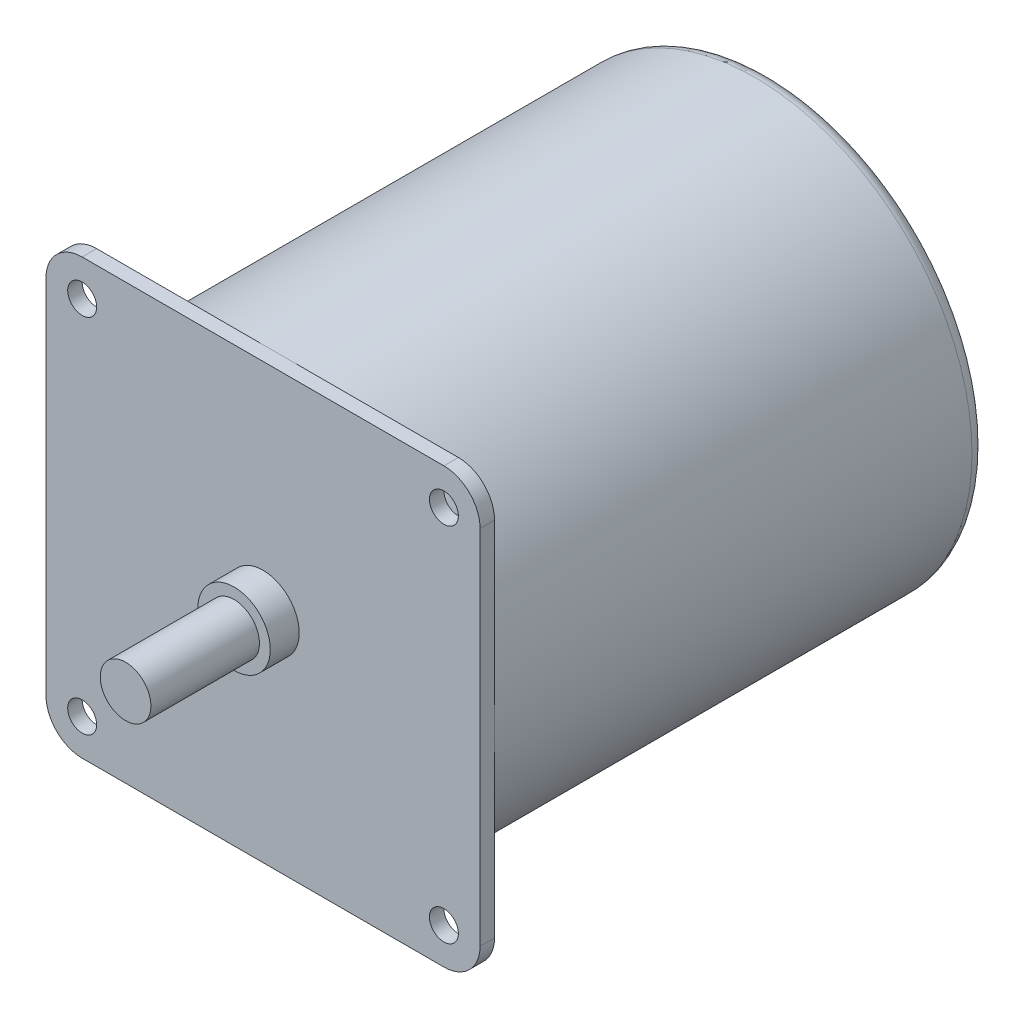
SolidWorks part; units mm, degrees
ref_plane "Front Plane" through (0, 0, 0) normal (0, 0, 1) x (1, 0, 0)
ref_plane "Top Plane" through (0, 0, 0) normal (0, 1, 0) x (1, 0, 0)
ref_plane "Right Plane" through (0, 0, 0) normal (1, 0, 0) x (0, 0, -1)
sketch "Sketch1" plane through (0, 0, 0) normal (0, 0, 1) x (1, 0, 0)
  circle A0 centre (0, 0) radius 30
  dimension "D1" = 60
extrude "Boss-Extrude1" add sketch "Sketch1" along normal blind 68
sketch "Sketch2" plane through (0, 0, 68) normal (0, 0, 1) x (1, 0, 0)
  line L0 (0, 33.5907) -> (0, -35.7587) construction
  line L1 (25, 30) -> (-25, 30)
  line L2 (30, 25) -> (30, -25)
  line L3 (25, -30) -> (-25, -30)
  line L4 (-30, 25) -> (-30, -25)
  line L5 (30, 30) -> (-30, -30) construction
  line L6 (30, -30) -> (-30, 30) construction
  line L7 (-22.9801, 0) -> (21.8103, 0) construction
  arc A1 (-25, -30) -> (-30, -25) centre (-25, -25) cw
  arc A2 (25, -30) -> (30, -25) centre (25, -25) ccw
  arc A3 (30, 25) -> (25, 30) centre (25, 25) ccw
  arc A4 (-25, 30) -> (-30, 25) centre (-25, 25) ccw
  circle A5 centre (-25, 25) radius 2
  circle A6 centre (25, 25) radius 2
  circle A7 centre (25, -25) radius 2
  circle A8 centre (-25, -25) radius 2
  point P0 (0, 0)
  dimension "D1" = 60
  dimension "D3" = 5
  dimension "D4" = 4
  dimension "D2" = 60
extrude "Boss-Extrude2" add sketch "Sketch2" along normal blind 2
fillet "Fillet1" radius 2 1 edges at (30, 0, 0)
sketch "Sketch3" plane through (0, 0, 70) normal (0, 0, 1) x (1, 0, 0)
  circle A0 centre (0, 0) radius 5
  dimension "D1" = 10
extrude "Boss-Extrude3" add sketch "Sketch3" along normal blind 4
sketch "Sketch4" plane through (0, 0, 74) normal (0, 0, 1) x (1, 0, 0)
  circle A0 centre (0, 0) radius 3.5
  dimension "D1" = 7
extrude "Boss-Extrude4" add sketch "Sketch4" along normal blind 15 separate body
